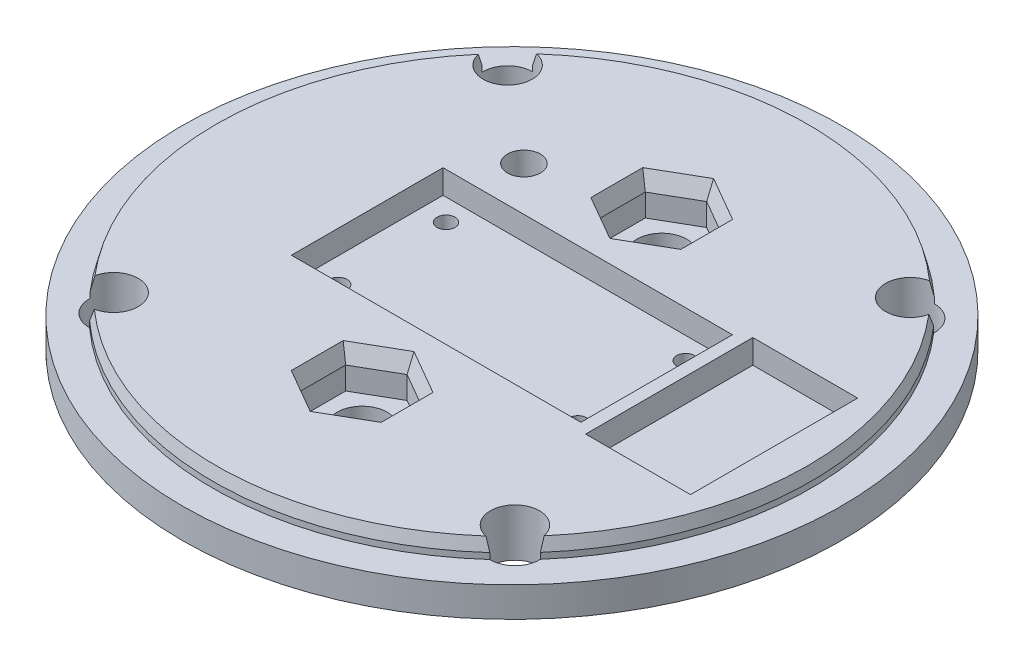
SolidWorks part; units mm, degrees
ref_plane "Спереди" through (0, 0, 0) normal (0, 0, 1) x (1, 0, 0)
ref_plane "Сверху" through (0, 0, 0) normal (0, 1, 0) x (1, 0, 0)
ref_plane "Справа" through (0, 0, 0) normal (1, 0, 0) x (0, 0, -1)
sketch "Эскиз1" plane through (0, 0, 0) normal (0, 1, 0) x (1, 0, 0)
  circle A0 centre (0, 0) radius 55
  dimension "D1" = 110
extrude "Бобышка-Вытянуть1" add sketch "Эскиз1" along normal blind 5
sketch "Эскиз2" plane through (0, 5, 0) normal (0, 1, 0) x (1, 0, 0)
  circle A0 centre (0, 0) radius 49.9
  dimension "D1" = 99.8
extrude "Бобышка-Вытянуть2" add sketch "Эскиз2" along normal blind 3
sketch "Эскиз3" plane through (0, 0, 0) normal (0, -1, 0) x (1, 0, 0)
  line L1 (17.5, -15) -> (-17.5, -15)
  line L2 (17.5, -15) -> (17.5, 15)
  line L3 (17.5, 15) -> (-17.5, 15)
  line L4 (-17.5, -15) -> (-17.5, 15)
  line L5 (17.5, -15) -> (-17.5, 15) construction
  line L6 (17.5, 15) -> (-17.5, -15) construction
  point P0 (0, 0)
  dimension "D1" = 35
  dimension "D2" = 30
extrude "Бобышка-Вытянуть3" add sketch "Эскиз3" along normal blind 25
sketch "Эскиз5" plane through (0, 0, 0) normal (0, -1, 0) x (1, 0, 0)
  line L0 (23.35, -22.85) -> (39.3102, -38.467) construction
  line L5 (-23.35, 22.85) -> (23.35, -22.85) construction
  line L6 (-23.35, -22.85) -> (23.35, 22.85) construction
  line L7 (-23.35, 22.85) -> (-39.3095, 38.4677) construction
  line L8 (23.35, 22.85) -> (39.1401, 38.6401) construction
  line L9 (-23.35, -22.85) -> (-39.3095, -38.4677) construction
  circle A0 centre (0, 0) radius 55 construction
  circle A1 centre (33.5922, -32.8719) radius 4.1
  circle A2 centre (-33.5917, -32.8724) radius 4.1
  circle A3 centre (-33.5917, 32.8724) radius 4.1
  circle A4 centre (33.4832, 32.9832) radius 4.1
  point P0 (0, 0)
  dimension "D3" = 8.2
  dimension "D8" = 91.24
  dimension "D1" = 46.7
  dimension "D2" = 45.7
  dimension "D4" = 8
  dimension "D5" = 8
  dimension "D6" = 8
  dimension "D7" = 8
extrude "Вырез-Вытянуть2" cut sketch "Эскиз5" against normal through all
sketch "Эскиз6" plane through (0, 8, 0) normal (0, 1, 0) x (1, 0, 0)
  line L0 (0, 0) -> (0.0004, 49.9) construction
  line L1 (0.0001, 20) -> (-17.9999, 20) construction
  arc A0 (33.5133, 36.9712) -> (-33.5128, 36.9717) centre (0, 0) ccw construction
  circle A1 centre (-17.9999, 20) radius 2.75
  dimension "D3" = 5.5
  dimension "D1" = 20
  dimension "D2" = 18
extrude "Вырез-Вытянуть3" cut sketch "Эскиз6" against normal through all
sketch "Sketch2" plane through (-17.5, 0, 0) normal (-1, 0, 0) x (0, 0, 1)
  line L0 (-15, -25) -> (15, 0) construction
  line L2 (10.125, -17.675) -> (-10.125, -17.675)
  line L3 (10.125, -17.675) -> (10.125, -7.325)
  line L4 (10.125, -7.325) -> (-10.125, -7.325)
  line L5 (-10.125, -17.675) -> (-10.125, -7.325)
  line L6 (10.125, -17.675) -> (-10.125, -7.325) construction
  line L7 (10.125, -7.325) -> (-10.125, -17.675) construction
  point P2 (0, -12.5)
  point P10 (0, -12.5)
  dimension "D1" = 20.25
  dimension "D2" = 10.35
extrude "Cut-Extrude1" cut sketch "Sketch2" against normal through all
sketch "Sketch3" plane through (0, 8, 0) normal (0, 1, 0) x (1, 0, 0)
  line L0 (49.9, 0) -> (-49.9, 0) construction
  line L2 (26.25, 13.95) -> (43.75, 13.95)
  line L3 (26.25, 13.95) -> (26.25, -13.95)
  line L4 (26.25, -13.95) -> (43.75, -13.95)
  line L5 (43.75, 13.95) -> (43.75, -13.95)
  line L6 (26.25, 13.95) -> (43.75, -13.95) construction
  line L7 (26.25, -13.95) -> (43.75, 13.95) construction
  line L8 (-24.15, 12.65) -> (24.15, 12.65)
  line L9 (-24.15, 12.65) -> (-24.15, -12.65)
  line L10 (-24.15, -12.65) -> (24.15, -12.65)
  line L11 (24.15, 12.65) -> (24.15, -12.65)
  line L12 (-24.15, 12.65) -> (24.15, -12.65) construction
  line L13 (-24.15, -12.65) -> (24.15, 12.65) construction
  arc A0 (37.5803, -32.8288) -> (37.6888, 32.7042) centre (0, 0) ccw construction
  arc A1 (-37.6883, 32.7048) -> (-37.6883, -32.7048) centre (0, 0) ccw construction
  point P8 (0, 0)
  point P13 (0, 0)
  point P22 (35, 0)
  dimension "D1" = 17.5
  dimension "D2" = 27.9
  dimension "D3" = 35
  dimension "D4" = 48.3
  dimension "D5" = 25.3
extrude "Cut-Extrude2" cut sketch "Sketch3" against normal blind 4
chamfer "Chamfer1" distance 2 angle 15 4 edges at (49.8999, 8, 0.0826) (-49.9, 8, 0) (0.0004, 8, -49.9) (-0.0824, 8, 49.8999)
sketch "Sketch4" plane through (0, -25, 0) normal (0, -1, 0) x (1, 0, 0)
  line L0 (-17.5, 0) -> (17.5, 0) construction
  line L1 (-17.5, 15) -> (-17.5, -15) construction
  line L2 (17.5, -15) -> (17.5, 15) construction
  line L4 (17.5, -15) -> (-17.5, -15)
  line L5 (17.5, -15) -> (17.5, 15)
  line L6 (17.5, 15) -> (-17.5, 15)
  line L7 (-17.5, -15) -> (-17.5, 15)
  line L8 (17.5, -15) -> (-17.5, 15) construction
  line L9 (17.5, 15) -> (-17.5, -15) construction
  point P6 (0, 0)
extrude "Cut-Extrude3" cut sketch "Sketch4" against normal blind 12.5
sketch "Sketch5" plane through (0, -7.325, 0) normal (0, -1, 0) x (1, 0, 0)
  line L0 (0, 10.125) -> (0, -10.125) construction
  line L1 (17.5, 10.125) -> (-17.5, 10.125) construction
  line L2 (17.5, -10.125) -> (-17.5, -10.125) construction
  line L4 (10, -35) -> (-10, -35)
  line L5 (10, -35) -> (10, 35)
  line L6 (10, 35) -> (-10, 35)
  line L7 (-10, -35) -> (-10, 35)
  line L8 (10, -35) -> (-10, 35) construction
  line L9 (10, 35) -> (-10, -35) construction
  point P6 (0, 0)
  dimension "D1" = 20
  dimension "D2" = 70
extrude "Boss-Extrude2" add sketch "Sketch5" against normal up to surface (5.325 mm away) from offset 2 up to face at (-17.9999, 0, -17.25) offset against normal yes
sketch "Sketch6" plane through (0, -5.325, 0) normal (0, -1, 0) x (1, 0, 0)
  line L0 (10, 25) -> (-10, 25) construction
  line L1 (10, 15) -> (10, 35) construction
  line L2 (-10, 35) -> (-10, 15) construction
  line L3 (10, -25) -> (-10, -25) construction
  line L4 (10, -35) -> (10, -15) construction
  line L5 (-10, -15) -> (-10, -35) construction
  circle A0 centre (0, 25) radius 4.15
  circle A1 centre (0, -25) radius 4.15
  dimension "D3" = 8.3
  dimension "D1" = 10
  dimension "D2" = 10
  dimension "D4" = 25
extrude "Cut-Extrude4" cut sketch "Sketch6" against normal through all
sketch "Sketch7" plane through (0, 8, 0) normal (0, 1, 0) x (1, 0, 0)
  line L1 (0, -32.5) -> (6.4952, -28.75)
  line L2 (6.4952, -28.75) -> (6.4952, -21.25)
  line L3 (6.4952, -21.25) -> (0, -17.5)
  line L4 (0, -17.5) -> (-6.4952, -21.25)
  line L5 (-6.4952, -21.25) -> (-6.4952, -28.75)
  line L6 (-6.4952, -28.75) -> (0, -32.5)
  line L7 (0, 17.5) -> (6.4952, 21.25)
  line L8 (6.4952, 21.25) -> (6.4952, 28.75)
  line L9 (6.4952, 28.75) -> (0, 32.5)
  line L10 (0, 32.5) -> (-6.4952, 28.75)
  line L11 (-6.4952, 28.75) -> (-6.4952, 21.25)
  line L12 (-6.4952, 21.25) -> (0, 17.5)
  circle A0 centre (0, -25) radius 7.5 construction
  circle A1 centre (0, 25) radius 7.5 construction
  dimension "D1" = 15
extrude "Cut-Extrude5" cut sketch "Sketch7" against normal blind 6.5
chamfer "Chamfer2" distance 1 angle 70 12 edges at (3.2476, 8, 19.375) (6.4952, 8, 25) (3.2476, 8, 30.625) (-3.2476, 8, 30.625) (-6.4952, 8, 25) (-3.2476, 8, 19.375) (3.2476, 8, -19.375) (6.4952, 8, -25) (3.2476, 8, -30.625) (-3.2476, 8, -30.625) (-6.4952, 8, -25) (-3.2476, 8, -19.375)
sketch "Sketch8" plane through (0, 4, 0) normal (0, 1, 0) x (1, 0, 0)
  line L0 (20, -12.65) -> (20, 12.65) construction
  line L1 (-24.15, -12.65) -> (24.15, -12.65) construction
  line L2 (24.15, 12.65) -> (-24.15, 12.65) construction
  line L3 (-20, 12.65) -> (-20, -12.65) construction
  line L4 (20, -12.65) -> (-20, 12.65) construction
  line L5 (20, 9) -> (-20, 9) construction
  line L6 (20, -9) -> (-20, -9) construction
  line L7 (0, 9) -> (0, -9) construction
  circle A0 centre (20, 9) radius 1.5
  circle A1 centre (20, -9) radius 1.5
  circle A2 centre (-20, 9) radius 1.5
  circle A3 centre (-20, -9) radius 1.5
  point P8 (0, 0)
  point P20 (0, 0)
  dimension "D2" = 3
  dimension "D1" = 40
  dimension "D3" = 18
extrude "Cut-Extrude6" cut sketch "Sketch8" against normal through all
